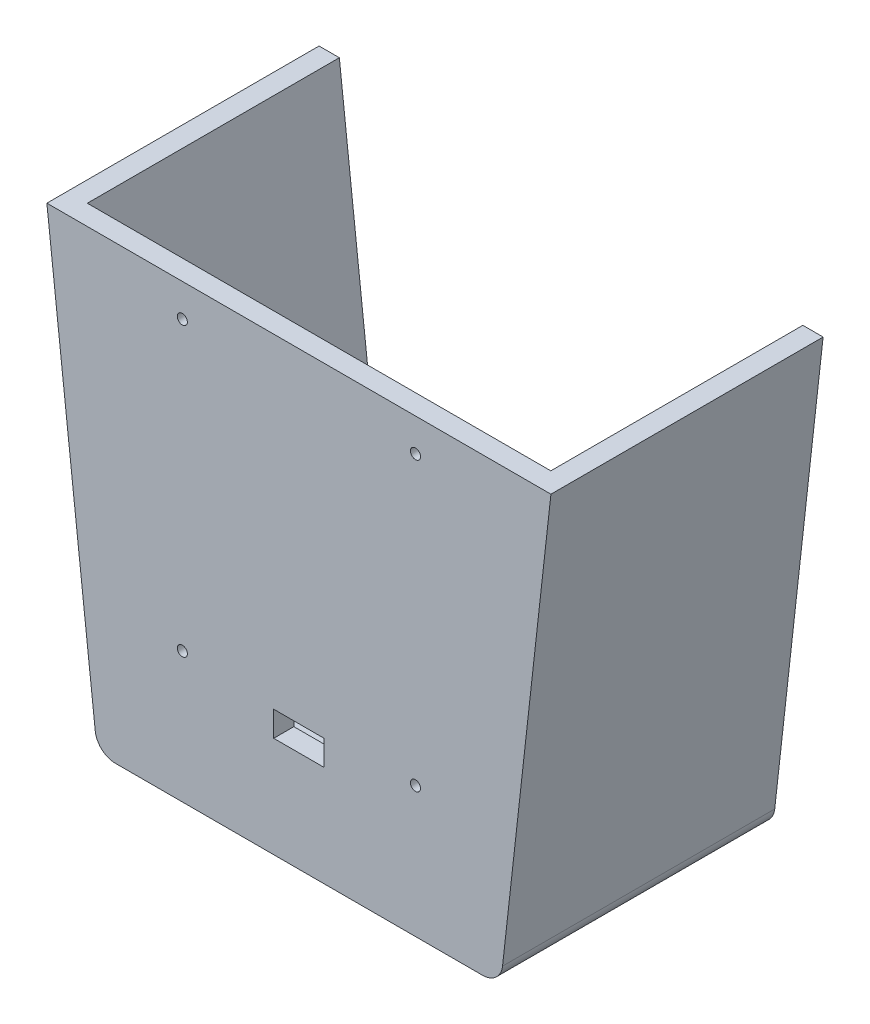
SolidWorks part; units mm, degrees
ref_plane "Front Plane" through (0, 0, 0) normal (0, 0, 1) x (1, 0, 0)
ref_plane "Top Plane" through (0, 0, 0) normal (0, 1, 0) x (1, 0, 0)
ref_plane "Right Plane" through (0, 0, 0) normal (1, 0, 0) x (0, 0, -1)
sketch "Sketch1" plane through (0, 0, 0) normal (0, 0, 1) x (1, 0, 0)
  line L0 (0, 56.7961) -> (0, -56.7961) construction
  line L1 (63.5, 56.7961) -> (-63.5, 56.7961)
  line L2 (-63.5, 56.7961) -> (-51.3049, -52.2806)
  line L3 (-46.2563, -56.7961) -> (46.2563, -56.7961)
  line L4 (63.5, 56.7961) -> (51.3049, -52.2806)
  line L5 (6.35, -25.0461) -> (-6.35, -25.0461)
  line L6 (-6.35, -25.0461) -> (-6.35, -31.3961)
  line L7 (-6.35, -31.3961) -> (6.35, -31.3961)
  line L8 (6.35, -25.0461) -> (6.35, -31.3961)
  arc A0 (-51.3049, -52.2806) -> (-46.2563, -56.7961) centre (-46.2563, -51.7161) ccw
  arc A1 (51.3049, -52.2806) -> (46.2563, -56.7961) centre (46.2563, -51.7161) cw
  point P10 (-50.8, -56.7961)
  point P16 (0, -31.3961)
  point P18 (0, -25.0461)
  dimension "D4" = 5.08
  dimension "D6" = 6.35
  dimension "D7" = 6.35
  dimension "D8" = 25.4
  dimension "D1" = 50.8
  dimension "D2" = 63.5
  dimension "D3" = 56.7961
  dimension "D5" = 109.0767
extrude "Boss-Extrude1" add sketch "Sketch1" against normal blind 5.08
sketch "Sketch2" plane through (0, 0, -5.08) normal (0, 0, 1) x (1, 0, 0)
  line L0 (0, 56.7961) -> (0, -56.7961) construction
  line L1 (63.5, 56.7961) -> (-63.5, 56.7961)
  line L2 (-63.5, 56.7961) -> (-51.3049, -52.2806)
  line L3 (-46.2563, -56.7961) -> (46.2563, -56.7961)
  line L4 (63.5, 56.7961) -> (51.3049, -52.2806)
  line L5 (6.35, -25.0461) -> (-6.35, -25.0461)
  line L6 (-6.35, -25.0461) -> (-6.35, -31.3961)
  line L7 (-6.35, -31.3961) -> (6.35, -31.3961)
  line L8 (6.35, -25.0461) -> (6.35, -31.3961)
  line L9 (-6.35, -25.0461) -> (-6.35, -31.3961) construction
  line L10 (6.35, -25.0461) -> (-6.35, -25.0461) construction
  line L12 (58.3883, 56.7961) -> (46.7612, -47.2006)
  line L13 (41.7126, -51.7161) -> (-41.7126, -51.7161)
  line L14 (-58.3883, 56.7961) -> (-46.7612, -47.2006)
  line L15 (63.5, 56.7961) -> (-63.5, 56.7961) construction
  arc A0 (-51.3049, -52.2806) -> (-46.2563, -56.7961) centre (-46.2563, -51.7161) ccw
  arc A1 (51.3049, -52.2806) -> (46.2563, -56.7961) centre (46.2563, -51.7161) cw
  arc A2 (46.7612, -47.2006) -> (41.7126, -51.7161) centre (41.7126, -46.6361) cw
  arc A3 (-46.7612, -47.2006) -> (-41.7126, -51.7161) centre (-41.7126, -46.6361) ccw
  point P10 (-50.8, -56.7961)
  point P16 (0, -31.3961)
  point P18 (0, -25.0461)
  point P30 (0, -51.7161)
  dimension "D4" = 5.08
  dimension "D6" = 6.35
  dimension "D7" = 6.35
  dimension "D8" = 25.4
  dimension "D9" = 0
  dimension "D10" = 5.08
  dimension "D1" = 50.8
  dimension "D2" = 63.5
  dimension "D5" = 109.0767
extrude "Boss-Extrude2" add sketch "Sketch2" against normal blind 63.5
sketch "Sketch4" plane through (0, 0, -5.08) normal (0, 0, -1) x (-1, 0, 0)
  line L0 (-20.32, 44.0961) -> (-20.32, -19.4039)
  line L1 (-20.32, -19.4039) -> (20.32, -19.4039)
  line L2 (-58.3883, 56.7961) -> (58.3883, 56.7961) construction
  line L3 (-20.32, 44.0961) -> (20.32, -19.4039)
  dimension "D1" = 12.7
  dimension "D2" = 63.5
  dimension "D3" = 40.64
  dimension "D4" = 38.0684
extrude "Boss-Extrude3" add sketch "Sketch4" along normal blind 10.16
ref_plane "Plane1" through (0, 0, -12.7) normal (0, 0, -1) x (-1, 0, 0)
sketch "Sketch7" plane through (0, 0, -12.7) normal (0, 0, -1) x (-1, 0, 0)
  line L0 (18.6944, -16.8639) -> (-17.78, -16.8639)
  line L1 (20.32, -19.4039) -> (-20.32, 44.0961) construction
  line L2 (-17.78, -16.8639) -> (-17.78, 40.1274)
  line L3 (20.32, -19.4039) -> (-20.32, 44.0961) construction
  line L4 (-17.78, 40.1274) -> (18.6944, -16.8639)
  line L5 (-20.32, 44.0961) -> (-20.32, -19.4039) construction
  line L6 (-20.32, -19.4039) -> (20.32, -19.4039) construction
  dimension "D1" = 2.54
  dimension "D2" = 2.54
extrude "Cut-Extrude1" cut sketch "Sketch7" against normal blind 7.62
sketch "Sketch9" plane through (0, 0, 0) normal (0, 0, 1) x (1, 0, 0)
  line L0 (63.5, 56.7961) -> (-63.5, 56.7961) construction
  line L1 (63.5, 56.7961) -> (29.3694, 56.7961) construction
  line L2 (29.3694, 56.7961) -> (29.3694, 48.5411) construction
  line L3 (0, 56.7961) -> (0, -56.7961) construction
  line L4 (-46.2563, -56.7961) -> (46.2563, -56.7961) construction
  circle A1 centre (29.3694, 48.5411) radius 1.27
  circle A2 centre (-29.3694, 48.5411) radius 1.27
  circle A3 centre (29.3694, -23.8489) radius 1.27
  circle A4 centre (-29.3694, -23.8489) radius 1.27
  dimension "D1" = 32.9473
  dimension "D2" = 2.54
  dimension "D3" = 32.9473
  dimension "D4" = 8.255
  dimension "D6" = 2.54
  dimension "D7" = 2.54
  dimension "D8" = 72.39
  dimension "D9" = 72.39
  dimension "D5" = 34.1306
extrude "Cut-Extrude2" cut sketch "Sketch9" against normal blind 5.08
